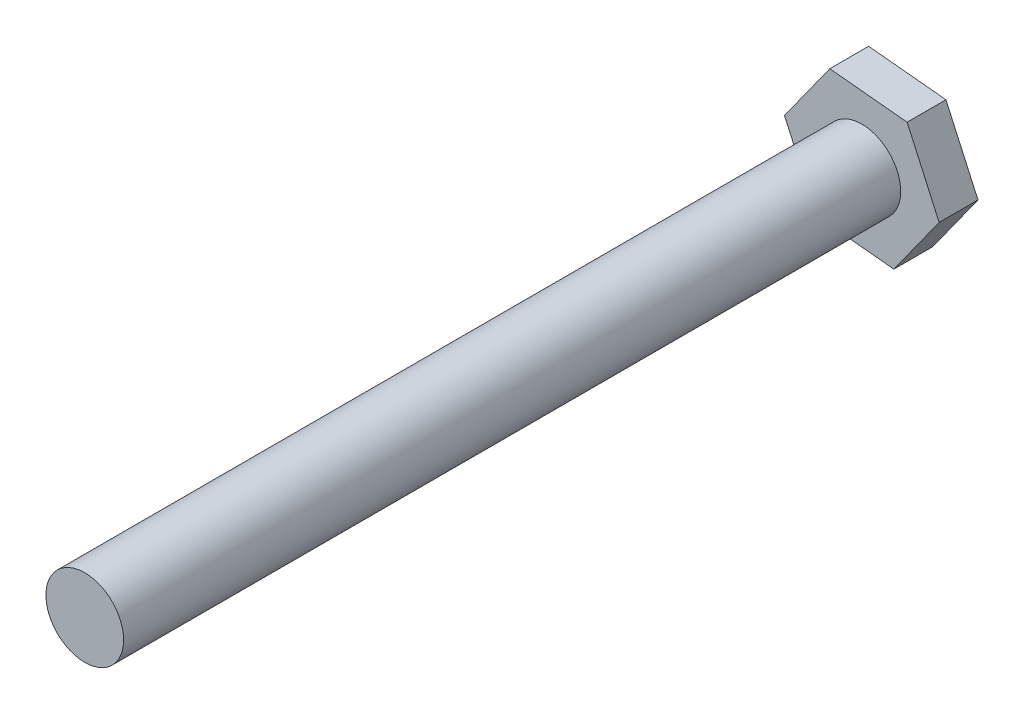
SolidWorks part; units mm, degrees
material "Brass"
ref_plane "Front Plane" through (0, 0, 0) normal (0, 0, 1) x (1, 0, 0)
ref_plane "Top Plane" through (0, 0, 0) normal (0, 1, 0) x (1, 0, 0)
ref_plane "Right Plane" through (0, 0, 0) normal (1, 0, 0) x (0, 0, -1)
sketch "Sketch1" plane through (0, 0, 0) normal (0, 0, 1) x (1, 0, 0)
  line L1 (3.4967, 4.8757) -> (-2.4741, 5.4661)
  line L2 (-2.4741, 5.4661) -> (-5.9709, 0.5904)
  line L3 (-5.9709, 0.5904) -> (-3.4967, -4.8757)
  line L4 (-3.4967, -4.8757) -> (2.4741, -5.4661)
  line L5 (2.4741, -5.4661) -> (5.9709, -0.5904)
  line L6 (5.9709, -0.5904) -> (3.4967, 4.8757)
  circle A0 centre (0, 0) radius 5.1962 construction
  dimension "D1" = 6
extrude "Boss-Extrude1" add sketch "Sketch1" along normal blind 3
sketch "Sketch2" plane through (0, 0, 3) normal (0, 0, 1) x (1, 0, 0)
  circle A0 centre (0, 0) radius 3
  dimension "D1" = 6
extrude "Boss-Extrude2" add sketch "Sketch2" along normal blind 60
